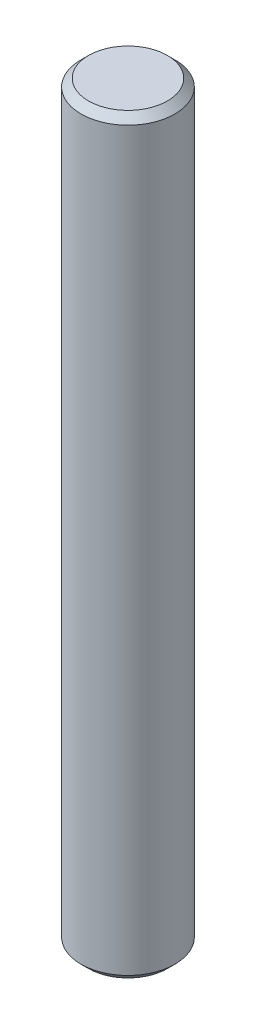
SolidWorks part; units mm, degrees
ref_plane "Front Plane" through (0, 0, 0) normal (0, 0, 1) x (1, 0, 0)
ref_plane "Top Plane" through (0, 0, 0) normal (0, 1, 0) x (1, 0, 0)
ref_plane "Right Plane" through (0, 0, 0) normal (1, 0, 0) x (0, 0, -1)
sketch "Sketch1" plane through (0, 0, 0) normal (0, 1, 0) x (1, 0, 0)
  circle A0 centre (0, 0) radius 12.5
extrude "Boss-Extrude1" add sketch "Sketch1" along normal mid plane 200
chamfer "Chamfer1" distance 2 angle 45 2 edges at (0, 100, 12.5) (0, -100, 12.5)
